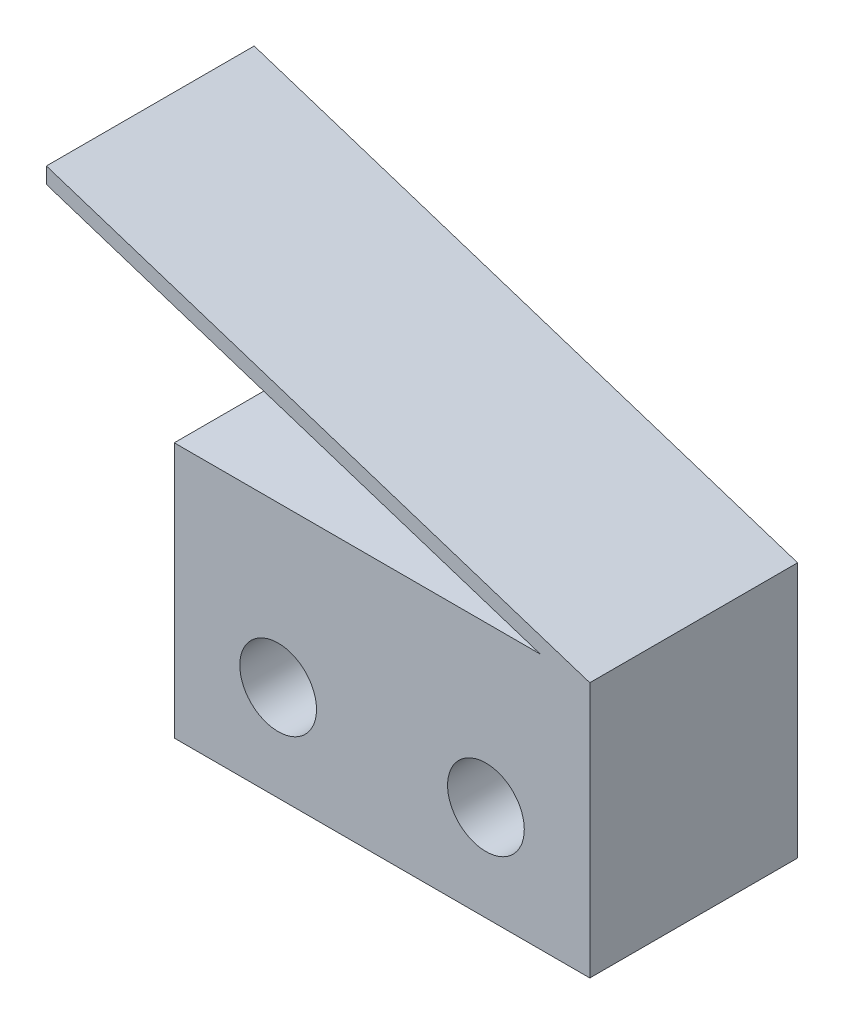
SolidWorks part; units mm, degrees
ref_plane "Ebene vorne" through (0, 0, 0) normal (0, 0, 1) x (1, 0, 0)
ref_plane "Ebene oben" through (0, 0, 0) normal (0, 1, 0) x (1, 0, 0)
ref_plane "Ebene rechts" through (0, 0, 0) normal (1, 0, 0) x (0, 0, -1)
sketch "Skizze1" plane through (0, 0, 0) normal (0, 0, 1) x (1, 0, 0)
  line L0 (0, 0) -> (13, 0)
  line L1 (13, 0) -> (13, 8)
  line L2 (13, 8) -> (-4, 13.5)
  line L3 (-4, 13.5) -> (-4, 13)
  line L4 (-4, 13) -> (11.4545, 8)
  line L5 (11.4545, 8) -> (0, 8)
  line L6 (0, 8) -> (0, 0)
  point P5 (0, 0)
  point P9 (-4, 13.66)
  dimension "D1" = 13
  dimension "D2" = 8
  dimension "D3" = 5
  dimension "D4" = 17
  dimension "D5" = 0.5
extrude "Aufsatz-Linear austragen1" add sketch "Skizze1" along normal blind 6.5
sketch "Skizze2" plane through (0, 0, 6.5) normal (0, 0, 1) x (1, 0, 0)
  line L0 (3.25, 3) -> (9.75, 3) construction
  line L1 (6.5, 3) -> (6.5, 0) construction
  line L2 (0, 0) -> (13, 0) construction
  line L3 (11.4545, 8) -> (0, 8) construction
  circle A0 centre (3.25, 3) radius 1.2
  circle A1 centre (9.75, 3) radius 1.2
  dimension "D1" = 2.4
  dimension "D2" = 6.5
  dimension "D3" = 5
extrude "Schnitt-Linear austragen1" cut sketch "Skizze2" against normal through all
